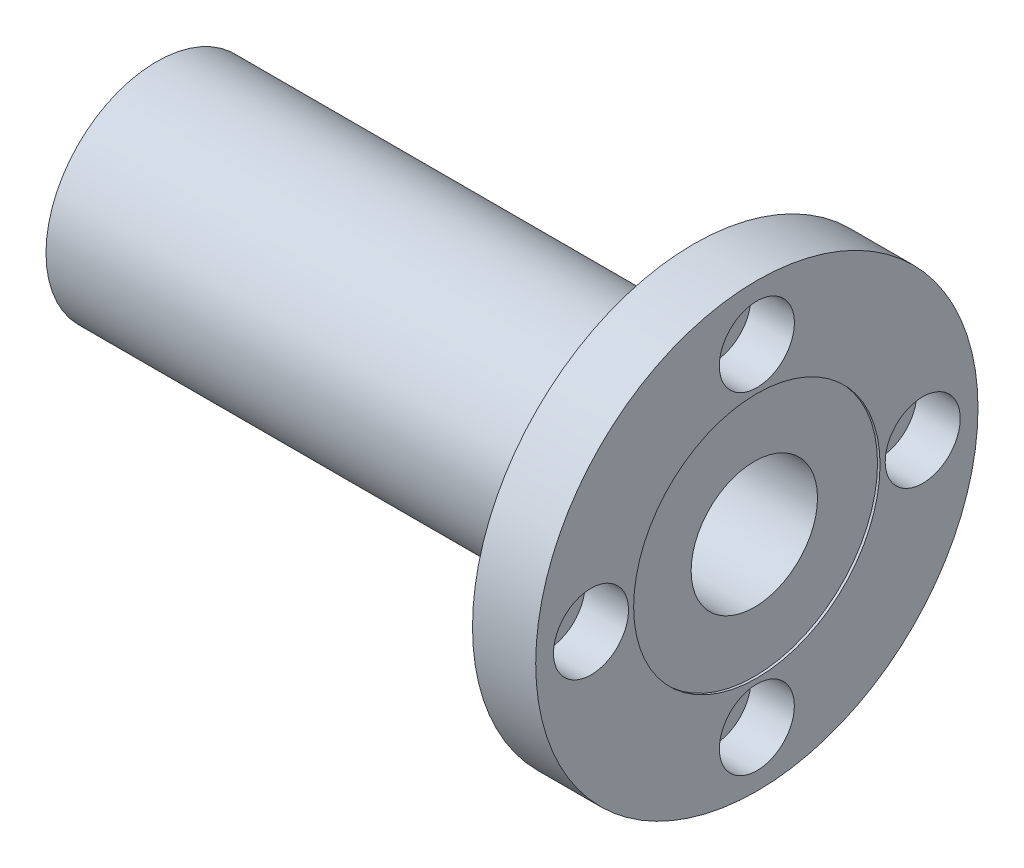
SolidWorks part; units mm, degrees
ref_plane "Front" through (0, 0, 0) normal (0, 0, 1) x (1, 0, 0)
ref_plane "Top" through (0, 0, 0) normal (0, 1, 0) x (1, 0, 0)
ref_plane "Right" through (0, 0, 0) normal (1, 0, 0) x (0, 0, -1)
sketch "Sketch1" plane through (0, 0, 0) normal (0, 0, 1) x (1, 0, 0)
  line L0 (-10.3908, 0) -> (15.4839, 0) construction
  line L1 (-30.1625, -11.1125) -> (23.8125, -11.1125)
  line L2 (23.8125, -11.1125) -> (23.8125, -22.225)
  line L3 (23.8125, -22.225) -> (30.1625, -22.225)
  line L4 (30.1625, -22.225) -> (30.1625, -6.35)
  line L5 (30.1625, -6.35) -> (-30.1625, -6.35)
  line L6 (-30.1625, -6.35) -> (-30.1625, -11.1125)
  line L8 (0, -8.5312) -> (0, 4.3394) construction
revolve "BASE-FLANGE" add sketch "Sketch1" angle 360 about L0
sketch "Sketch10" plane through (0, 0, 0) normal (0, 0, 1) x (1, 0, 0)
  line L1 (-2.9889, 0) -> (22.217, 0) construction
  line L2 (30.1625, -22.225) -> (30.1625, 22.225) construction
  line L3 (7.2053, 16.6688) -> (18.9423, 16.6688) construction
  line L4 (30.1625, 20.4394) -> (25.7962, 20.4394)
  line L6 (25.7962, 20.4394) -> (25.7962, 19.05)
  line L7 (25.7962, 19.05) -> (23.8125, 19.05)
  line L8 (23.8125, 22.225) -> (23.8125, -22.225) construction
  line L9 (23.8125, 19.05) -> (23.8125, 16.6688)
  line L10 (30.1625, 20.4394) -> (30.1625, 16.6688)
  line L11 (30.1625, 16.6688) -> (23.8125, 16.6688)
  point P0 (30.1625, 16.6688)
  dimension "Diameter [PCD]" = 33.3375
  dimension "Depth [Z]" = 4.3663
  dimension "Hole Diameter [Y]" = 7.5413
  dimension "Hole Diameter [X]" = 4.7625
revolve "MOUNTING-HOLE" cut sketch "Sketch10" angle 360 about L3
pattern_circular "MOUNTING-HOLE PATTERN" count 4 every 90 about axis through (0, 0, 0) along (1, 0, 0) of "MOUNTING-HOLE"
sketch "Sketch7" plane through (30.1625, 0, 0) normal (1, 0, 0) x (0, 0, -1)
  circle A0 centre (0, 0) radius 11.1125 construction
  point P3 (0, 11.1125)
  dimension "D1" = 22.225
sketch "Sketch9" plane through (30.1625, 0, 0) normal (1, 0, 0) x (0, 0, -1)
  circle A0 centre (0, 0) radius 12.3825
extrude "SHAFT DIA" cut sketch "Sketch9" against normal blind 0.254
equation "\"D1@Sketch9\" = \"Outside Diameter [DD]@Sketch1\"+.1"
